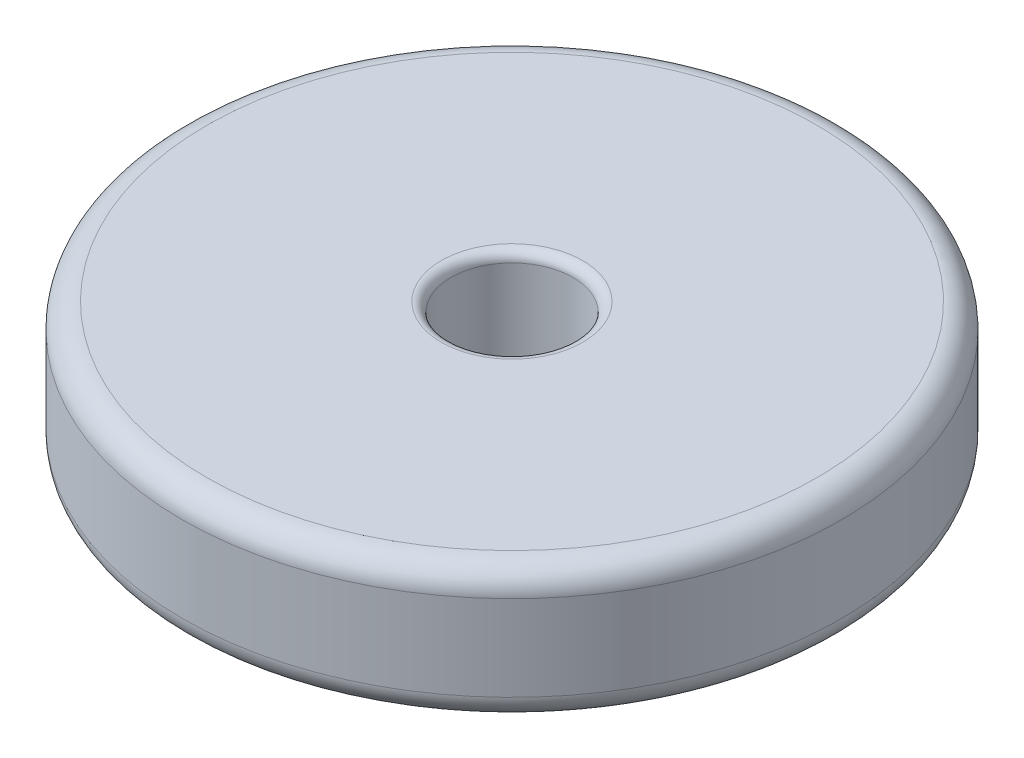
SolidWorks part; units mm, degrees
ref_plane "Front Plane" through (0, 0, 0) normal (0, 0, 1) x (1, 0, 0)
ref_plane "Top Plane" through (0, 0, 0) normal (0, 1, 0) x (1, 0, 0)
ref_plane "Right Plane" through (0, 0, 0) normal (1, 0, 0) x (0, 0, -1)
sketch "Sketch1" plane through (0, 0, 0) normal (0, 1, 0) x (1, 0, 0)
  circle A0 centre (0, 0) radius 85.725
  circle A1 centre (0, 0) radius 15.875
  dimension "D1" = 171.45
  dimension "D2" = 31.75
extrude "Boss-Extrude1" add sketch "Sketch1" along normal blind 34.925
fillet "Fillet1" radius 6.35 2 edges at (0, 0, 85.725) (0, 34.925, 85.725)
fillet "Fillet2" radius 2.54 2 edges at (0, 0, 15.875) (0, 34.925, 15.875)
